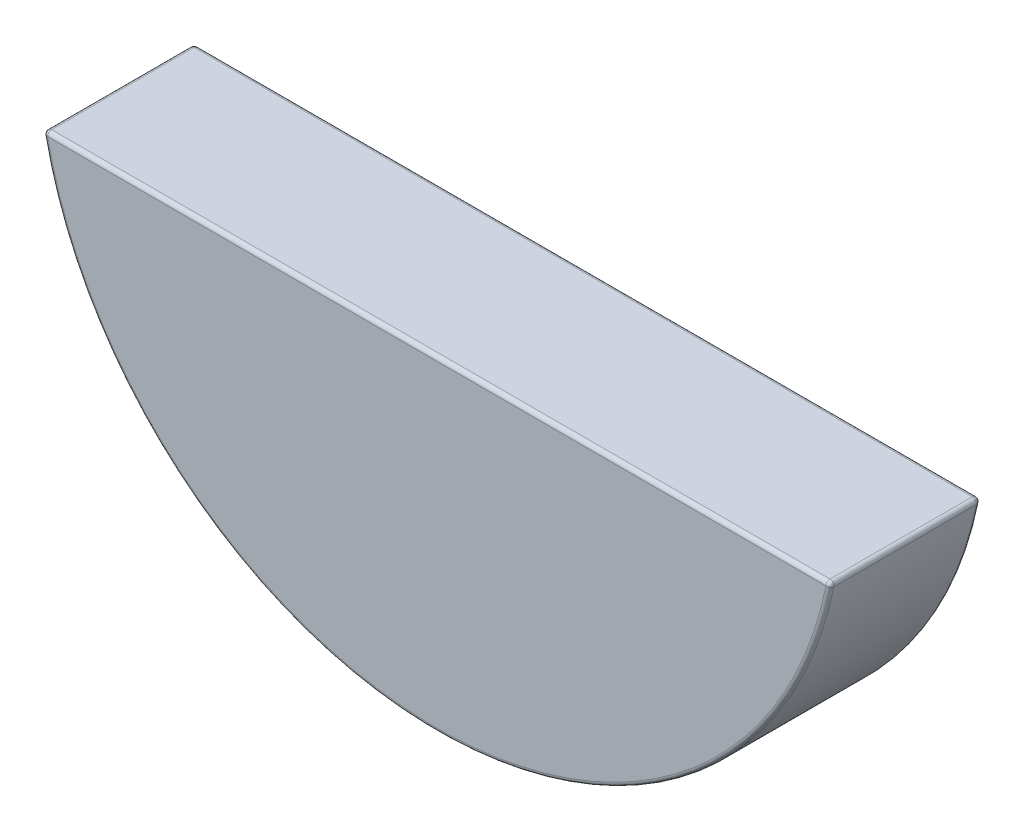
SolidWorks part; units mm, degrees
ref_plane "Front Plane" through (0, 0, 0) normal (0, 0, 1) x (1, 0, 0)
ref_plane "Top Plane" through (0, 0, 0) normal (0, 1, 0) x (1, 0, 0)
ref_plane "Right Plane" through (0, 0, 0) normal (1, 0, 0) x (0, 0, -1)
sketch "Sketch1" plane through (0, 0, 0) normal (0, 0, 1) x (1, 0, 0)
  line L0 (-73.722, 0) -> (74.6512, 0) construction
  line L1 (-6.2368, -1.1938) -> (6.2368, -1.1938)
  arc A0 (-6.2368, -1.1938) -> (6.2368, -1.1938) centre (0, 0) ccw
  dimension "Breadth" = 12.7
  dimension "Excursion" = 1.1938
extrude "Extrude1" add sketch "Sketch1" along normal blind 2.3813
fillet "Fillet3" radius 0.0635 6 edges at (-6.2368, -1.1938, 1.1906) (6.2368, -1.1938, 1.1906) (0, -1.1938, 2.3813) (0, -6.35, 2.3813) (0, -1.1938, 0) (0, -6.35, 0)
sketch "Sketch3" plane through (0, 0, 0) normal (0, 0, 1) x (1, 0, 0)
  line L0 (-50.8, -5.969) -> (50.8, -5.969)
  line L2 (-6.1595, -1.1938) -> (6.1595, -1.1938) construction
  dimension "D1" = 50.8
  dimension "D2" = 101.6
  dimension "High" = 4.7752
extrude "Cut-Extrude2" [suppressed] cut sketch "Sketch3" along normal through all and the other way through all flip side to cut
sketch "Sketch2" plane through (0, 0, 0) normal (0, 0, 1) x (1, 0, 0)
  line L0 (-2.54, 0) -> (-2.54, -50.8)
  line L1 (0, 0) -> (0, -50.8) construction
  dimension "D1" = 50.8
  dimension "Length" = 5.08
extrude "Cut-Extrude1" [suppressed] cut sketch "Sketch2" against normal through all and the other way through all flip side to cut
mirror "Mirror1" [suppressed] about plane through (0, 0, 0) normal (1, 0, 0)
equation "\"Radius@Fillet3\" = \"Width@Extrude1\"*2/75"
